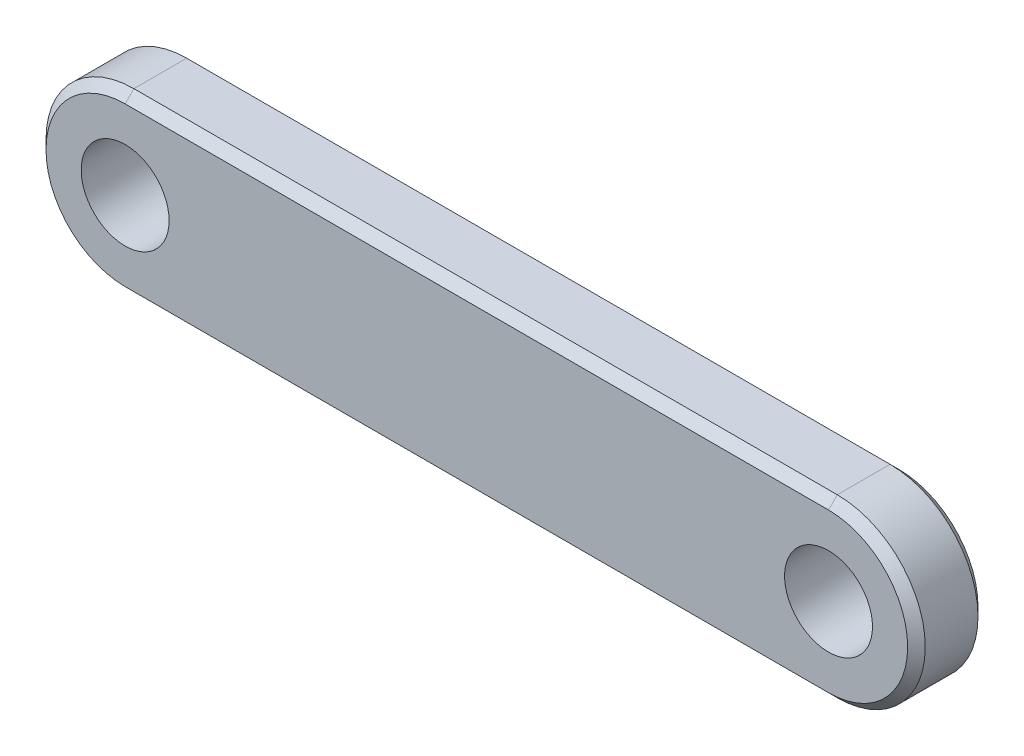
SolidWorks part; units mm, degrees
material "Plain Carbon Steel"
ref_plane "Front Plane" through (0, 0, 0) normal (0, 0, 1) x (1, 0, 0)
ref_plane "Top Plane" through (0, 0, 0) normal (0, 1, 0) x (1, 0, 0)
ref_plane "Right Plane" through (0, 0, 0) normal (1, 0, 0) x (0, 0, -1)
sketch "Sketch1" plane through (0, 0, 0) normal (0, 0, 1) x (1, 0, 0)
  line L0 (-20, 0) -> (20, 0) construction
  line L1 (-20, 5) -> (20, 5)
  line L2 (-20, -5) -> (20, -5)
  arc A0 (-20, 5) -> (-20, -5) centre (-20, 0) ccw
  arc A1 (20, -5) -> (20, 5) centre (20, 0) ccw
  circle A2 centre (-20, 0) radius 2.5
  circle A3 centre (20, 0) radius 2.5
  point P3 (0, 0)
  dimension "D3" = 5
  dimension "D1" = 5
  dimension "D2" = 40
extrude "Boss-Extrude1" add sketch "Sketch1" against normal blind 4
chamfer "Chamfer1" distance 0.5 angle 45 8 edges at (0, -5, -4) (25, 0, -4) (-25, 0, -4) (0, 5, -4) (0, -5, 0) (25, 0, 0) (-25, 0, 0) (0, 5, 0)
